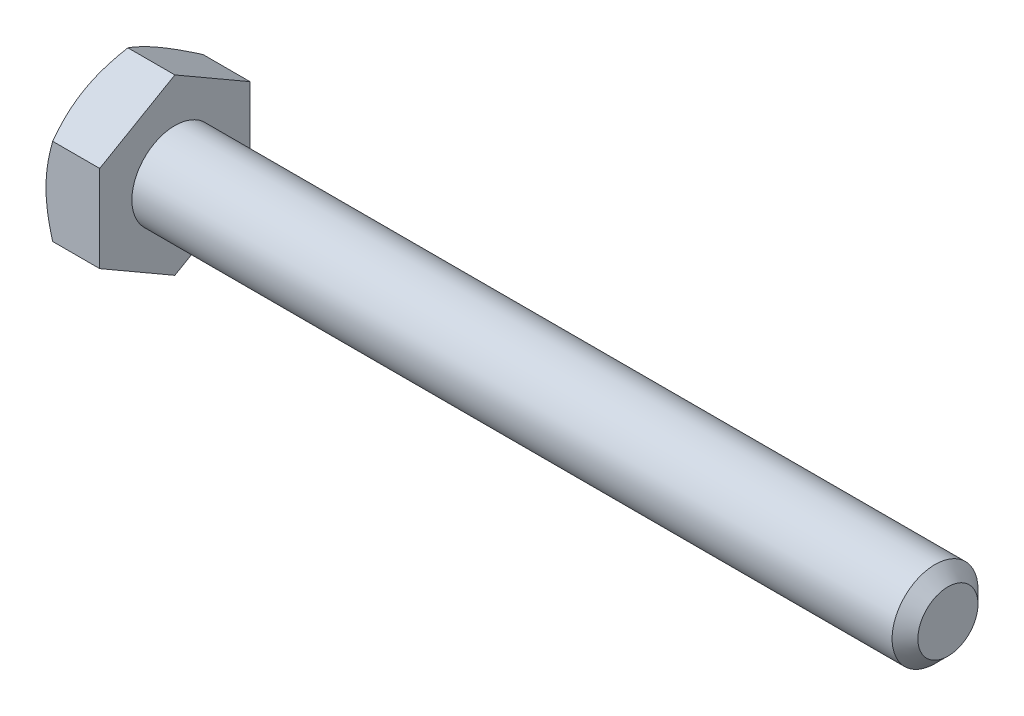
SolidWorks part; units mm, degrees
material "Alloy Steel"
ref_plane "Front Plane" through (0, 0, 0) normal (0, 0, 1) x (1, 0, 0)
ref_plane "Top Plane" through (0, 0, 0) normal (0, 1, 0) x (1, 0, 0)
ref_plane "Right Plane" through (0, 0, 0) normal (1, 0, 0) x (0, 0, -1)
sketch "Sketch1" plane through (0, 0, 0) normal (0, 0, 1) x (1, 0, 0)
  line L0 (-30.5594, 0) -> (30.5594, 0) construction
  line L1 (30.5594, 3.175) -> (30.5594, -3.175) construction
  line L2 (-26.5906, 5.5562) -> (-26.5906, -5.5562) construction
  line L3 (-30.5594, 5.5562) -> (-30.5594, -5.5562) construction
  point P9 (-26.5906, 0)
  point P10 (26.1144, -3.175)
  dimension "D1" = 4.445
  dimension "Screw Dia" = 6.35
  dimension "Hex" = 11.1125
  dimension "Head Ht" = 3.9688
  dimension "Screw Lenght" = 57.15
ref_plane "Plane2" through (30.5594, 0, 0) normal (1, 0, 0) x (0, 0, -1)
sketch "Sketch5" plane through (30.5594, 0, 0) normal (1, 0, 0) x (0, 0, -1)
  circle A0 centre (0, 0) radius 3.175
extrude "Boss-Extrude3" add sketch "Sketch5" against normal up to vertex (57.15 mm away) up to point (-26.5906, 0, 0)
sketch "Sketch9" plane through (30.5594, 0, 0) normal (1, 0, 0) x (0, 0, -1)
  circle A1 centre (0, 0) radius 3.175
  circle A2 centre (0, 0) radius 3.175
  dimension "D1" = 0
curve "Helix/Spiral1" pitch 1.27 height 20.32 turns 16 parameters "Pitch"=1.27
chamfer "Chamfer1" distance 0.9525 angle 45 1 edges at (30.5594, 0, -3.175)
sketch "Sketch10" plane through (0, 0, 0) normal (0, 0, 1) x (1, 0, 0)
  line L0 (30.5594, 3.175) -> (31.0356, 2.3501)
  line L1 (31.0356, 2.3501) -> (31.1944, 2.3501)
  line L2 (31.1944, 2.3501) -> (31.6706, 3.175)
  line L3 (30.5594, 3.175) -> (31.6706, 3.175)
  line L4 (31.115, 3.175) -> (31.115, 2.3501) construction
  line L5 (30.7975, 2.7626) -> (31.4325, 2.7626) construction
  dimension "D1" = 60
  dimension "D2" = 0.1588
  dimension "D3" = 0.635
sketch "Sketch11" plane through (0, 0, 0) normal (0, 0, 1) x (1, 0, 0)
  line L0 (-26.5906, 3.175) -> (-26.5906, 0)
  line L1 (-26.5906, 0) -> (14.6844, 0)
  line L3 (14.6844, 0) -> (11.5094, 3.175)
  line L4 (-26.5906, 3.175) -> (11.5094, 3.175)
  dimension "D1" = 45
  dimension "MIn Thread" = 19.05
revolve "Revolve1" add sketch "Sketch11" angle 360 about L1
sketch "Sketch6" plane through (-26.5906, 0, 0) normal (-1, 0, 0) x (0, 0, 1)
  line L0 (0, 5.5562) -> (0, -5.5562) construction
  line L1 (5.5563, 3.2079) -> (0, 6.4158)
  line L2 (0, 6.4158) -> (-5.5562, 3.2079)
  line L3 (-5.5562, 3.2079) -> (-5.5562, -3.2079)
  line L4 (-5.5562, -3.2079) -> (0, -6.4158)
  line L5 (0, -6.4158) -> (5.5563, -3.2079)
  line L6 (5.5563, -3.2079) -> (5.5563, 3.2079)
  circle A0 centre (0, 0) radius 5.5563 construction
extrude "Boss-Extrude4" add sketch "Sketch6" along normal up to vertex (3.9688 mm away) up to point (-30.5594, -5.5562, 0)
sketch "Sketch7" plane through (-30.5594, 0, 0) normal (-1, 0, 0) x (0, 0, 1)
  circle A0 centre (0, 0) radius 5.5563 construction
  circle A1 centre (0, 0) radius 5.5563
sketch "Sketch8" plane through (-30.5594, 0, 0) normal (-1, 0, 0) x (0, 0, 1)
  circle A0 centre (0, 0) radius 5.5563 construction
  circle A1 centre (0, 0) radius 5.5563
extrude "Cut-Extrude3" cut sketch "Sketch8" against normal through all draft 60 flip side to cut
sketch "Sketch12" plane through (-30.5594, 0, 0) normal (-1, 0, 0) x (0, 0, 1)
  line L0 (0, 4.2783) -> (0, 2.3892) construction
  line L1 (0.1667, 4.2783) -> (0.1667, 2.3892)
  line L2 (-0.1667, 4.2783) -> (-0.1667, 2.3892)
  line L3 (0, 3.175) -> (0, -3.175) construction
  arc A0 (0.1667, 4.2783) -> (-0.1667, 4.2783) centre (0, 4.2783) ccw
  arc A1 (-0.1667, 2.3892) -> (0.1667, 2.3892) centre (0, 2.3892) ccw
  circle A3 centre (0, 0) radius 2.2225 construction
  circle A4 centre (0, 0) radius 4.445 construction
  point P2 (0, 3.3337)
  dimension "D1" = 4.445
  dimension "D3" = 8.89
  dimension "D2" = 0.3334
extrude "Cut-Extrude4" cut sketch "Sketch12" against normal blind 0.254
pattern_circular "CirPattern1" count 3 over 360 about axis through (0, 0, 0) along (1, 0, 0) of "Cut-Extrude4"
equation "\"D2@Sketch10\" = \"Pitch@Helix/Spiral1\"*.125"
equation "\"D3@Sketch10\" = \"Pitch@Helix/Spiral1\"*.5"
equation "\"D3@Helix/Spiral1\" = \"MIn Thread@Sketch11\"+\"Pitch@Helix/Spiral1\""
equation "\"D1@Chamfer1\" = \"Pitch@Helix/Spiral1\"*.75"
equation "\"D1@Sketch12\" = \"Hex@Sketch1\"*.4"
equation "\"D3@Sketch12\" = \"Hex@Sketch1\"*.8"
equation "\"D2@Sketch12\" = \"Hex@Sketch1\"*.03"
equation "\"D1@Sketch1\" = \"Pitch@Helix/Spiral1\"*3.5"
